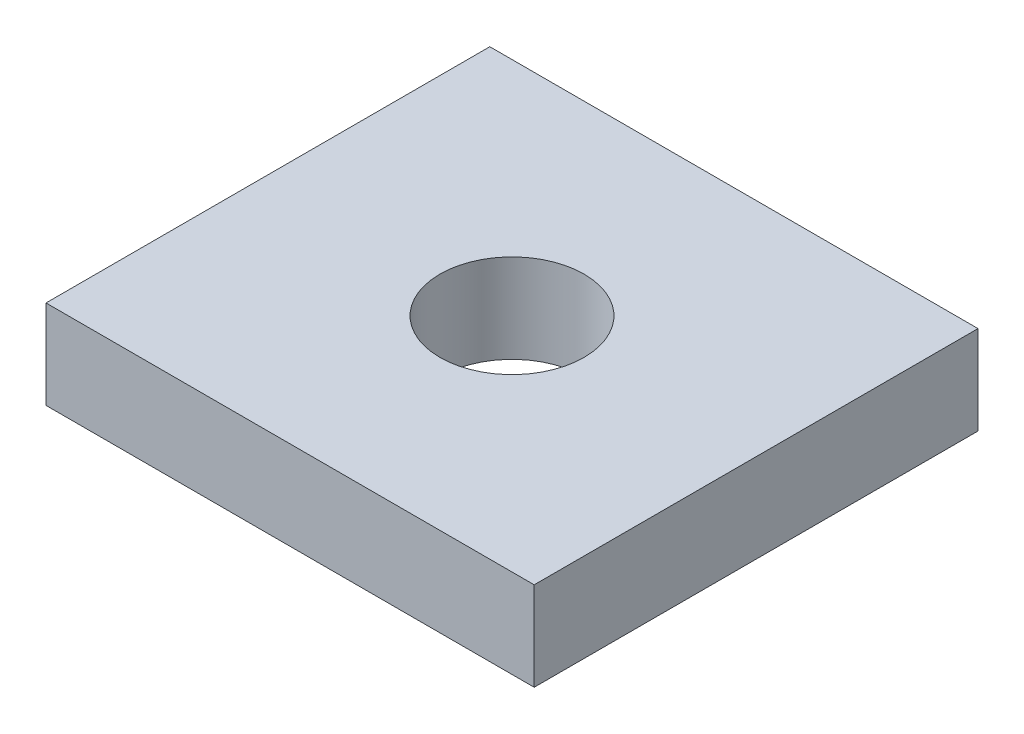
SolidWorks part; units mm, degrees
material "POLYURETHANE (11671)"
ref_plane "Plan de face" through (0, 0, 0) normal (0, 0, 1) x (1, 0, 0)
ref_plane "Plan de dessus" through (0, 0, 0) normal (0, 1, 0) x (1, 0, 0)
ref_plane "Plan de droite" through (0, 0, 0) normal (1, 0, 0) x (0, 0, -1)
sketch "Esquisse2" plane through (0, 0, 0) normal (0, 1, 0) x (1, 0, 0)
  line L1 (-11, 10) -> (11, 10)
  line L2 (-11, 10) -> (-11, -10)
  line L3 (-11, -10) -> (11, -10)
  line L4 (11, 10) -> (11, -10)
  circle A0 centre (0, 0) radius 3.25
  point P4 (-11, 0)
  point P5 (0, 10)
  dimension "D3" = 6.5
  dimension "D1" = 22
  dimension "D2" = 20
extrude "Boss.-Extru.1" add sketch "Esquisse2" along normal blind 4
